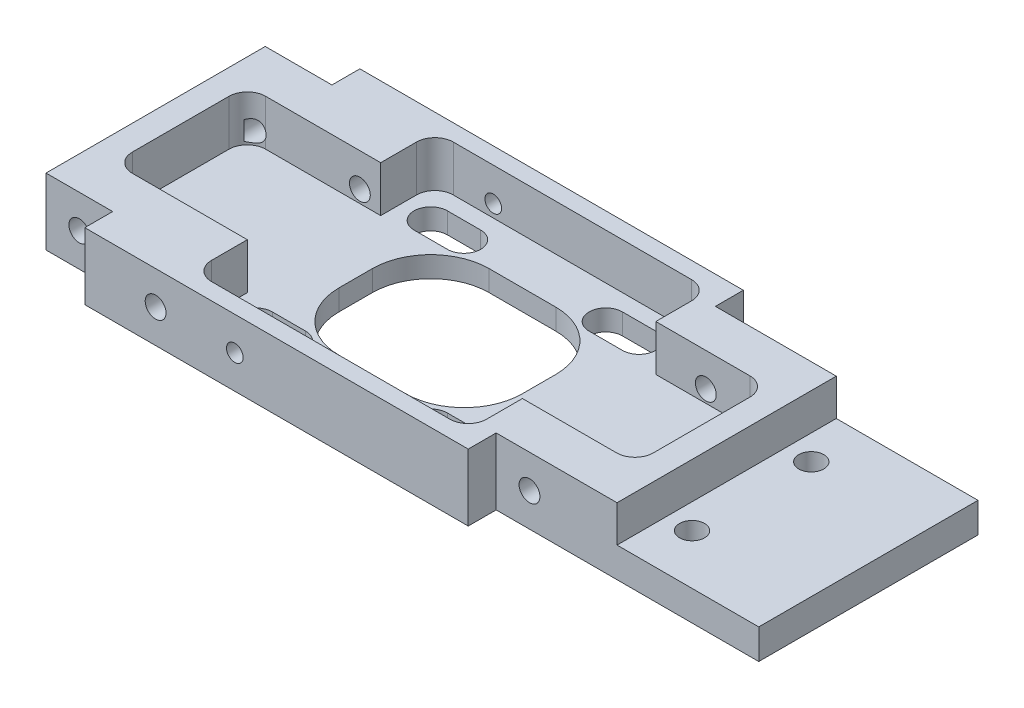
SolidWorks part; units mm, degrees
ref_plane "Спереди" through (0, 0, 0) normal (0, 0, 1) x (1, 0, 0)
ref_plane "Сверху" through (0, 0, 0) normal (0, 1, 0) x (1, 0, 0)
ref_plane "Справа" through (0, 0, 0) normal (1, 0, 0) x (0, 0, -1)
sketch "Эскиз1" plane through (0, 0, 0) normal (0, 1, 0) x (1, 0, 0)
  line L0 (-23, 16.5) -> (23, 16.5)
  line L1 (-78.3446, 0) -> (76.7639, 0) construction
  line L2 (-23, -16.5) -> (23, -16.5)
  line L3 (0, 71.639) -> (0, -91.0231) construction
  line L4 (-23, 16.5) -> (-23, 13.15)
  line L5 (-23, -16.5) -> (-23, -13.15)
  line L6 (23, 16.5) -> (23, 13.15)
  line L7 (23, -16.5) -> (23, -13.15)
  line L8 (-23, 13.15) -> (-31, 13.15)
  line L9 (-23, -13.15) -> (-31, -13.15)
  line L10 (-31, 13.15) -> (-31, -13.15)
  line L11 (23, 13.15) -> (54.5, 13.15)
  line L12 (23, -13.15) -> (54.5, -13.15)
  line L13 (54.5, 13.15) -> (54.5, -13.15)
  circle A0 centre (40.5, 7.15) radius 1.5
  circle A1 centre (40.5, -7.15) radius 1.5
  dimension "D8" = 3
  dimension "D1" = 46
  dimension "D2" = 23
  dimension "D3" = 13.15
  dimension "D4" = 3.35
  dimension "D5" = 3.35
  dimension "D6" = 8
  dimension "D7" = 31.5
  dimension "D9" = 14
  dimension "D10" = 6
extrude "Бобышка-Вытянуть1" add sketch "Эскиз1" along normal blind 8
sketch "Эскиз2" plane through (0, 8, 0) normal (0, 1, 0) x (1, 0, 0)
  line L0 (37.5, 13.15) -> (37.5, -13.15)
  line L1 (54.5, 13.15) -> (23, 13.15) construction
  line L2 (23, -13.15) -> (54.5, -13.15) construction
  line L3 (37.5, -13.15) -> (54.5, -13.15)
  line L4 (54.5, -13.15) -> (54.5, 13.15)
  line L5 (54.5, 13.15) -> (37.5, 13.15)
  dimension "D1" = 17
extrude "Вырез-Вытянуть1" cut sketch "Эскиз2" against normal blind 4.4
sketch "Эскиз3" plane through (0, 8, 0) normal (0, 1, 0) x (1, 0, 0)
  line L0 (-95.2544, 0) -> (112.8615, 0) construction
  line L1 (-25.7952, -8) -> (-12, -8)
  line L2 (-12, -8) -> (-12, -12.2952)
  line L3 (-9.7952, -14.5) -> (18.7952, -14.5)
  line L4 (21, -12.2952) -> (21, -8)
  line L5 (21, -8) -> (32.2952, -8)
  line L7 (21, 8) -> (32.2952, 8)
  line L8 (21, 12.2952) -> (21, 8)
  line L9 (-12, 8) -> (-12, 12.2952)
  line L10 (-9.7952, 14.5) -> (18.7952, 14.5)
  line L11 (-25.7952, 8) -> (-12, 8)
  line L12 (-28, 5.7952) -> (-28, -5.7952)
  line L13 (34.5, 5.7952) -> (34.5, -5.7952)
  arc A0 (-25.7952, 8) -> (-28, 5.7952) centre (-25.7952, 5.7952) ccw
  arc A1 (-28, -5.7952) -> (-25.7952, -8) centre (-25.7952, -5.7952) ccw
  arc A2 (-12, -12.2952) -> (-9.7952, -14.5) centre (-9.7952, -12.2952) ccw
  arc A3 (18.7952, -14.5) -> (21, -12.2952) centre (18.7952, -12.2952) ccw
  arc A4 (32.2952, -8) -> (34.5, -5.7952) centre (32.2952, -5.7952) ccw
  arc A5 (34.5, 5.7952) -> (32.2952, 8) centre (32.2952, 5.7952) ccw
  arc A6 (21, 12.2952) -> (18.7952, 14.5) centre (18.7952, 12.2952) ccw
  arc A7 (-9.7952, 14.5) -> (-12, 12.2952) centre (-9.7952, 12.2952) ccw
  dimension "D8" = 2.2048
  dimension "D1" = 8
  dimension "D2" = 8
  dimension "D3" = 14.5
  dimension "D4" = 19
extrude "Вырез-Вытянуть3" cut sketch "Эскиз3" against normal blind 5.5
sketch "Эскиз6" plane through (0, 2.5, 0) normal (0, 1, 0) x (1, 0, 0)
  line L2 (-7, 2) -> (-7, -2)
  line L5 (0, 9) -> (8, 9)
  line L6 (15, 2) -> (15, -2)
  line L7 (8, -9) -> (0, -9)
  arc A0 (0, -9) -> (-7, -2) centre (0, -2) cw
  arc A1 (8, -9) -> (15, -2) centre (8, -2) ccw
  arc A2 (15, 2) -> (8, 9) centre (8, 2) ccw
  arc A3 (0, 9) -> (-7, 2) centre (0, 2) ccw
  dimension "D2" = 7
  dimension "D1" = 9
  dimension "D3" = 7
  dimension "D4" = 15
  dimension "D5" = 9
extrude "Вырез-Вытянуть4" cut sketch "Эскиз6" against normal through all
sketch "Эскиз7" plane through (0, 2.5, 0) normal (0, 1, 0) x (1, 0, 0)
  line L0 (18.5, 37.5688) -> (18.5, -29.9313) construction
  line L1 (54.5, -13.15) -> (54.5, 13.15) construction
  line L2 (10.5, 47.981) -> (10.5, -37.1121) construction
  line L3 (-59.0946, 10.5) -> (80.2141, 10.5) construction
  line L4 (14.5, 18.087) -> (14.5, 7.5509) construction
  line L5 (12.5, 12.5) -> (16.5, 12.5)
  line L6 (12.5, 8.5) -> (16.5, 8.5)
  line L7 (-96.1264, 0) -> (138.4082, 0) construction
  line L8 (10.5, 12.5) -> (18.5, 12.5) construction
  line L9 (18.5, 8.5) -> (10.5, 8.5) construction
  line L10 (4, 34.1432) -> (4, -42.6559) construction
  line L11 (-4.5, 8.5) -> (-8.5, 8.5)
  line L12 (-4.5, 12.5) -> (-8.5, 12.5)
  line L13 (12.5, -8.5) -> (16.5, -8.5)
  line L14 (12.5, -12.5) -> (16.5, -12.5)
  line L15 (-4.5, -8.5) -> (-8.5, -8.5)
  line L16 (-4.5, -12.5) -> (-8.5, -12.5)
  arc A0 (12.5, 8.5) -> (12.5, 12.5) centre (12.5, 10.5) cw
  arc A1 (16.5, 8.5) -> (16.5, 12.5) centre (16.5, 10.5) ccw
  arc A2 (-8.5, 8.5) -> (-8.5, 12.5) centre (-8.5, 10.5) cw
  arc A3 (-4.5, 8.5) -> (-4.5, 12.5) centre (-4.5, 10.5) ccw
  arc A4 (16.5, -8.5) -> (16.5, -12.5) centre (16.5, -10.5) cw
  arc A5 (12.5, -8.5) -> (12.5, -12.5) centre (12.5, -10.5) ccw
  arc A6 (-4.5, -8.5) -> (-4.5, -12.5) centre (-4.5, -10.5) cw
  arc A7 (-8.5, -8.5) -> (-8.5, -12.5) centre (-8.5, -10.5) ccw
  dimension "D8" = 2
  dimension "D1" = 36
  dimension "D2" = 44
  dimension "D3" = 10.5
  dimension "D4" = 4
  dimension "D5" = 8
  dimension "D6" = 2
  dimension "D7" = 4
  dimension "D9" = 10.5
  dimension "D10" = 6.5
extrude "Вырез-Вытянуть5" cut sketch "Эскиз7" against normal through all
sketch "Эскиз9" plane through (0, 0, 13.15) normal (0, 0, 1) x (1, 0, 0)
  circle A0 centre (-27, 4) radius 1.25
  dimension "D1" = 2.5
  dimension "D2" = 4
  dimension "D3" = 4
extrude "Вырез-Вытянуть6" cut sketch "Эскиз9" against normal blind 6
sketch "Эскиз10" plane through (0, 0, -13.15) normal (0, 0, -1) x (-1, 0, 0)
  circle A0 centre (27, 4) radius 1.25
  dimension "D1" = 2.5
  dimension "D2" = 4
  dimension "D3" = 4
extrude "Вырез-Вытянуть7" cut sketch "Эскиз10" against normal blind 6
sketch "Эскиз11" plane through (0, 0, -13.15) normal (0, 0, -1) x (-1, 0, 0)
  circle A0 centre (-27, 4) radius 1.25
  dimension "D1" = 2.5
  dimension "D2" = 4
  dimension "D3" = 4
extrude "Вырез-Вытянуть8" cut sketch "Эскиз11" against normal blind 6
sketch "Эскиз12" plane through (0, 0, 13.15) normal (0, 0, 1) x (1, 0, 0)
  circle A0 centre (27, 4) radius 1.25
  dimension "D1" = 2.5
  dimension "D2" = 4
  dimension "D3" = 4
extrude "Вырез-Вытянуть9" cut sketch "Эскиз12" against normal blind 6
sketch "Эскиз13" plane through (0, 0, 16.5) normal (0, 0, 1) x (1, 0, 0)
  circle A0 centre (-5, 4) radius 1
  circle A1 centre (-14.5, 4) radius 1.25
  dimension "D1" = 2.5
  dimension "D4" = 2
  dimension "D2" = 4
  dimension "D3" = 16.5
  dimension "D5" = 4
  dimension "D6" = 18
extrude "Вырез-Вытянуть10" cut sketch "Эскиз13" against normal blind 46
